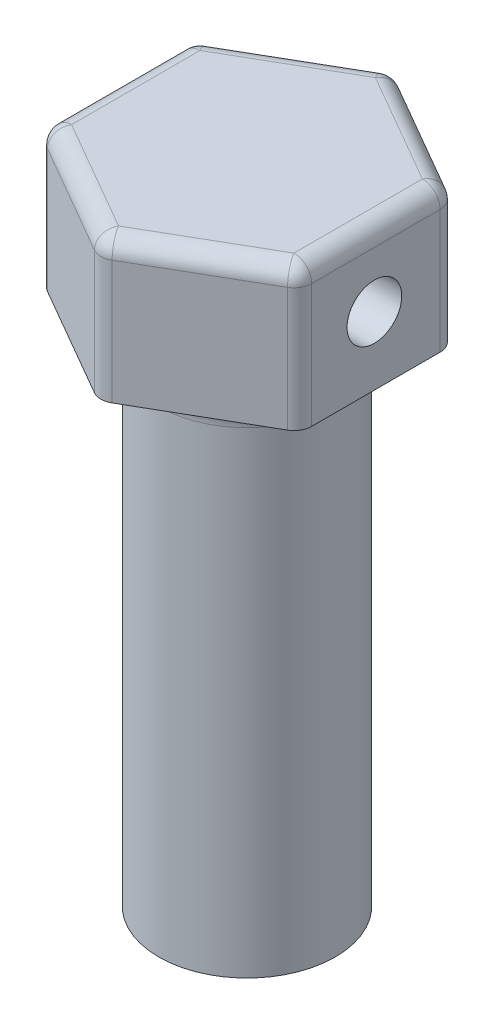
SolidWorks part; units mm, degrees
ref_plane "Front Plane" through (0, 0, 0) normal (0, 0, 1) x (1, 0, 0)
ref_plane "Top Plane" through (0, 0, 0) normal (0, 1, 0) x (1, 0, 0)
ref_plane "Right Plane" through (0, 0, 0) normal (1, 0, 0) x (0, 0, -1)
sketch "Sketch1" plane through (0, 0, 0) normal (0, 1, 0) x (1, 0, 0)
  line L1 (7.3, -4.2147) -> (7.3, 4.2147)
  line L2 (7.3, 4.2147) -> (0, 8.4293)
  line L3 (0, 8.4293) -> (-7.3, 4.2147)
  line L4 (-7.3, 4.2147) -> (-7.3, -4.2147)
  line L5 (-7.3, -4.2147) -> (0, -8.4293)
  line L6 (0, -8.4293) -> (7.3, -4.2147)
  circle A0 centre (0, 0) radius 7.3 construction
  dimension "D1" = 14.6
extrude "Boss-Extrude1" add sketch "Sketch1" along normal blind 8
sketch "Sketch2" plane through (0, 0, 0) normal (0, -1, 0) x (1, 0, 0)
  line L0 (-1.5, 1.4518) -> (-1.5, -1.4518)
  line L1 (-7.3, -4.2147) -> (-7.3, 4.2147) construction
  arc A0 (-1.5, -1.4518) -> (-1.5, 1.4518) centre (0, 0) ccw
  circle A1 centre (0, 0) radius 5
  dimension "D1" = 4.175
  dimension "D2" = 10
  dimension "D3" = 1.5
extrude "Boss-Extrude2" add sketch "Sketch2" along normal blind 29 contours A1 | A0 L0
fillet "Fillet1" radius 2 1 edges at (0, 0, 5)
sketch "Sketch3" plane through (7.3, 0, 0) normal (1, 0, 0) x (0, 0, -1)
  line L0 (-7, 0) -> (7, 0) construction
  line L1 (4.2147, 8) -> (4.2147, 0) construction
  circle A0 centre (-0.0853, 3.85) radius 1.55
  dimension "D1" = 3.1
  dimension "D2" = 3.85
  dimension "D3" = 4.3
extrude "Cut-Extrude1" cut sketch "Sketch3" against normal through all
fillet "Fillet2" radius 1 12 edges at (-3.65, 8, 6.322) (-7.3, 8, 0) (-3.65, 8, -6.322) (3.65, 8, -6.322) (7.3, 8, 0) (3.65, 8, 6.322) (-7.3, 4, -4.2147) (0, 4, -8.4293) (7.3, 4, -4.2147) (7.3, 4, 4.2147) (0, 4, 8.4293) (-7.3, 4, 4.2147)
sketch "Sketch4" plane through (0, 0, 0) normal (1, 0, 0) x (0, 0, -1)
  line L1 (-16.1086, 1.5942) -> (18.1695, 1.5942)
  line L2 (-16.1086, 1.5942) -> (-16.1086, -34.824)
  line L3 (-16.1086, -34.824) -> (18.1695, -34.824)
  line L4 (18.1695, 1.5942) -> (18.1695, -34.824)
extrude "Cut-Extrude2" [suppressed] cut sketch "Sketch4" against normal through all both and the other way through all
sketch "Sketch5" plane through (0, -29, 0) normal (0, -1, 0) x (1, 0, 0)
  circle A0 centre (0, 0) radius 2.0875
  dimension "D1" = 4.175
extrude "Cut-Extrude3" cut sketch "Sketch5" against normal blind 3
sketch "Sketch6" plane through (0, 0, 0) normal (0, -1, 0) x (1, 0, 0)
  circle A0 centre (0, 0) radius 1.25
  dimension "D1" = 2.5
extrude "Cut-Extrude4" cut sketch "Sketch6" against normal up to surface (3.063 mm away)
sketch "Sketch7" plane through (3.65, 0, -6.322) normal (0.5, 0, -0.866) x (-0.866, 0, -0.5)
  line L0 (-3.6373, 3.5) -> (3.6373, 3.5) construction
  line L1 (-3.6373, 7) -> (-3.6373, 0) construction
  line L2 (3.6373, 0) -> (3.6373, 7) construction
  circle A0 centre (0, 3.5) radius 0.5
  point P8 (0, 0)
  point P9 (0, 0)
  point P10 (-1.2301, 3.5)
  point P11 (0, 3.5)
  dimension "D1" = 1
extrude "Cut-Extrude5" cut sketch "Sketch7" against normal blind 0.5
